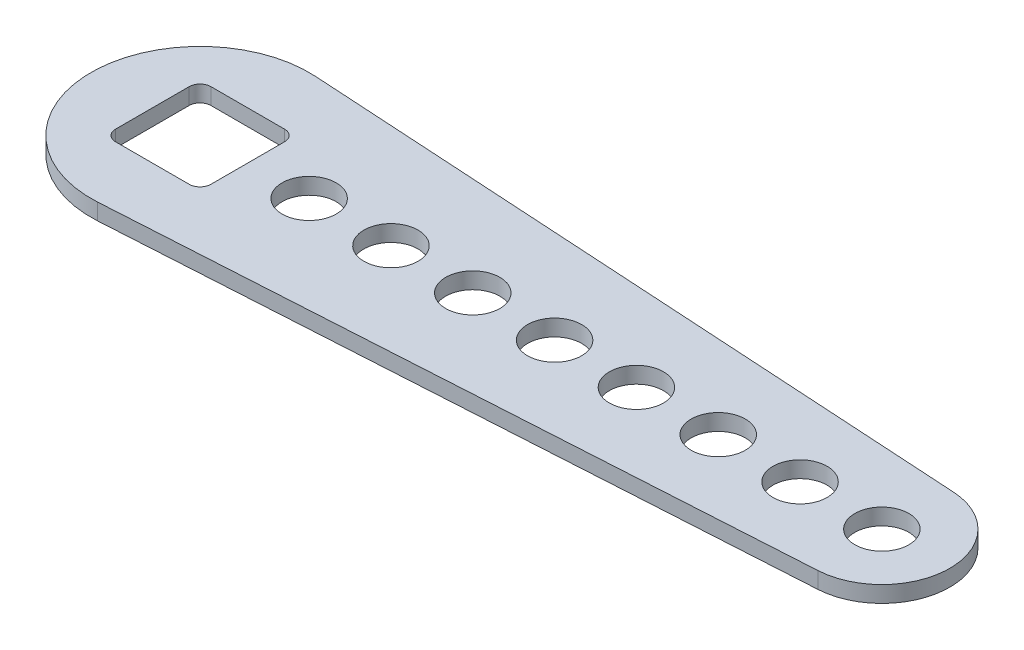
SolidWorks part; units mm, degrees
ref_plane "Front Plane" through (0, 0, 0) normal (0, 0, 1) x (1, 0, 0)
ref_plane "Top Plane" through (0, 0, 0) normal (0, 1, 0) x (1, 0, 0)
ref_plane "Right Plane" through (0, 0, 0) normal (1, 0, 0) x (0, 0, -1)
sketch "Sketch1" plane through (0, 0, 0) normal (0, 1, 0) x (1, 0, 0)
  line L0 (0.965, 15.9709) -> (100.6012, 9.9506)
  line L1 (-5.4, 7) -> (5.4, 7)
  line L2 (-7, 5.4) -> (-7, -5.4)
  line L3 (-5.4, -7) -> (5.4, -7)
  line L4 (7, 5.4) -> (7, -5.4)
  line L5 (-7, 7) -> (7, -7) construction
  line L6 (-7, -7) -> (7, 7) construction
  line L7 (0.965, -15.9709) -> (100.6012, -9.9506)
  line L8 (16, 0) -> (28, 0) construction
  arc A0 (0.965, 15.9709) -> (0.965, -15.9709) centre (0, 0) ccw
  circle A1 centre (16, 0) radius 3.9688
  circle A2 centre (28, 0) radius 3.9688
  circle A3 centre (40, 0) radius 3.9687
  circle A4 centre (52, 0) radius 3.9688
  circle A5 centre (64, 0) radius 3.9688
  circle A6 centre (76, 0) radius 3.9688
  arc A7 (100.6012, 9.9506) -> (100.6012, -9.9506) centre (100, 0) cw
  arc A8 (-7, -5.4) -> (-5.4, -7) centre (-5.4, -5.4) ccw
  arc A9 (5.4, -7) -> (7, -5.4) centre (5.4, -5.4) ccw
  arc A10 (5.4, 7) -> (7, 5.4) centre (5.4, 5.4) cw
  arc A11 (-5.4, 7) -> (-7, 5.4) centre (-5.4, 5.4) ccw
  circle A12 centre (88, 0) radius 3.9688
  circle A13 centre (100, 0) radius 3.9688
  point P0 (0, 0)
  dimension "D2" = 7.9375
  dimension "D4" = 6
  dimension "D5" = 16
  dimension "D8" = 1.6
  dimension "D1" = 14
  dimension "D6" = 16
  dimension "D7" = 12
  dimension "D3" = 8
extrude "Boss-Extrude1" add sketch "Sketch1" along normal blind 2.4
